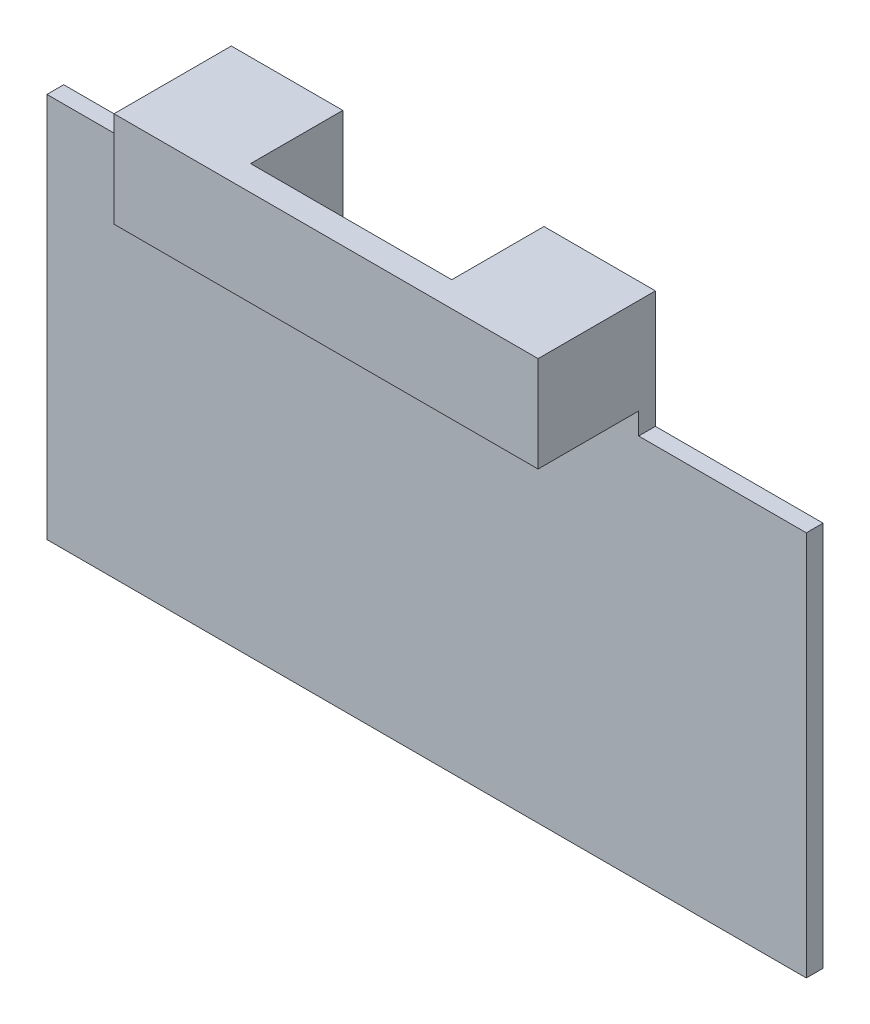
SolidWorks part; units mm, degrees
ref_plane "Front Plane" through (0, 0, 0) normal (0, 0, 1) x (1, 0, 0)
ref_plane "Top Plane" through (0, 0, 0) normal (0, 1, 0) x (1, 0, 0)
ref_plane "Right Plane" through (0, 0, 0) normal (1, 0, 0) x (0, 0, -1)
sketch "Sketch1" plane through (0, 0, 0) normal (0, 0, 1) x (1, 0, 0)
  line L1 (-17.0592, 26.3772) -> (28.2408, 26.3772)
  line L2 (-17.0592, 26.3772) -> (-17.0592, -3.6228)
  line L3 (-17.0592, -3.6228) -> (28.2408, -3.6228)
  line L4 (28.2408, 26.3772) -> (28.2408, -3.6228)
  dimension "D1" = 45.3
  dimension "D2" = 30
extrude "Boss-Extrude1" add sketch "Sketch1" along normal blind 7
sketch "Sketch2" plane through (0, 0, 7) normal (0, 0, 1) x (1, 0, 0)
  line L0 (-17.0592, 26.3772) -> (-17.0592, -3.6228) construction
  line L1 (-17.0592, 20.6716) -> (28.2408, 20.6716)
  line L2 (-17.0592, 20.6716) -> (-17.0592, -3.6228)
  line L3 (-17.0592, -3.6228) -> (28.2408, -3.6228)
  line L4 (28.2408, 20.6716) -> (28.2408, -3.6228)
extrude "Cut-Extrude1" cut sketch "Sketch2" against normal blind 6
sketch "Sketch5" plane through (0, 26.3772, 0) normal (0, 1, 0) x (1, 0, 0)
  line L0 (28.2408, 0) -> (-17.0592, 0) construction
  line L1 (-0.4092, 0) -> (11.5908, 0)
  line L2 (-0.4092, 0) -> (-0.4092, -5.5)
  line L3 (-0.4092, -5.5) -> (11.5908, -5.5)
  line L4 (11.5908, 0) -> (11.5908, -5.5)
  line L6 (-0.4092, -4.1493) -> (-17.0592, -4.1493) construction
  line L7 (-17.0592, -7) -> (-17.0592, 0) construction
  line L8 (11.5908, -4.1493) -> (28.2408, -4.1493) construction
  line L9 (28.2408, -7) -> (28.2408, 0) construction
  line L10 (28.2408, -7) -> (-17.0592, -7) construction
  line L11 (-17.0592, 0) -> (-7.0592, 0)
  line L12 (-17.0592, 0) -> (-17.0592, -7)
  line L13 (-17.0592, -7) -> (-7.0592, -7)
  line L14 (-7.0592, 0) -> (-7.0592, -7)
  line L15 (28.2408, -7) -> (18.2408, -7)
  line L20 (28.2408, -7) -> (28.2408, 0)
  line L21 (28.2408, 0) -> (18.2408, 0)
  line L22 (18.2408, -7) -> (18.2408, 0)
  dimension "D1" = 5.5
  dimension "D2" = 12
  dimension "D3" = 10
  dimension "D4" = 7
  dimension "D5" = 7
  dimension "D6" = 10
extrude "Cut-Extrude2" cut sketch "Sketch5" against normal blind 7
